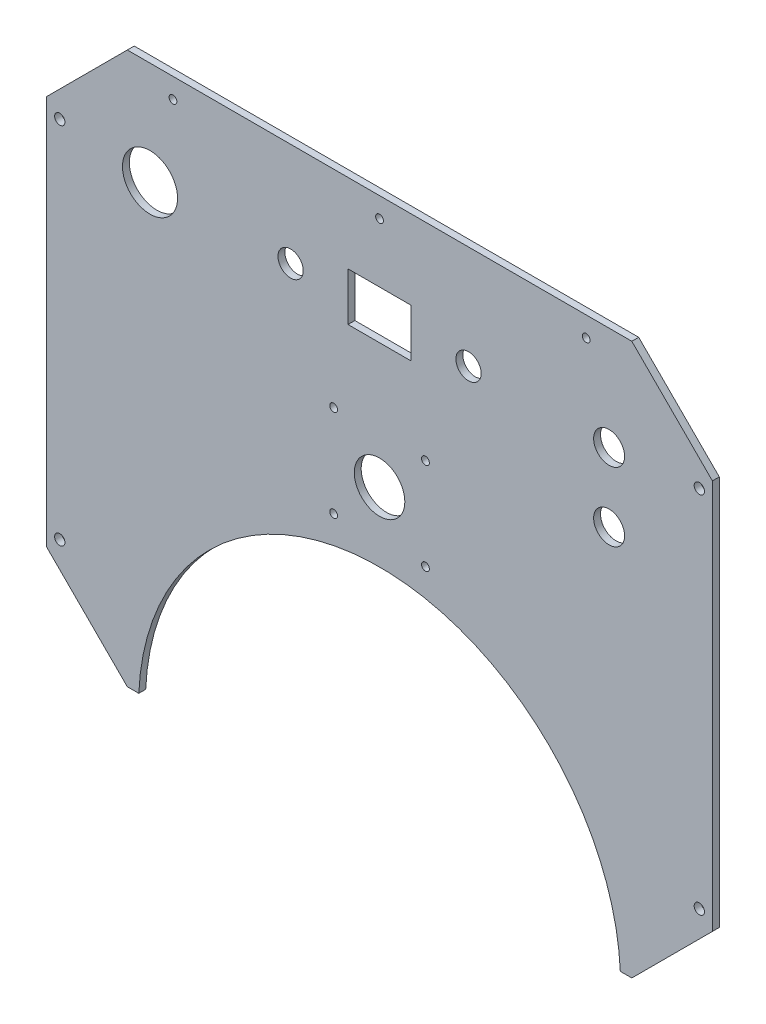
SolidWorks part; units mm, degrees
ref_plane "Plan de face" through (0, 0, 0) normal (0, 0, 1) x (1, 0, 0)
ref_plane "Plan de dessus" through (0, 0, 0) normal (0, 1, 0) x (1, 0, 0)
ref_plane "Plan de droite" through (0, 0, 0) normal (1, 0, 0) x (0, 0, -1)
sketch "Esquisse1" plane through (0, 0, 0) normal (0, 0, 1) x (1, 0, 0)
  line L0 (-145, 85) -> (-109.8862, 120.1138)
  line L1 (-109.8862, 120.1138) -> (-105, 125) construction
  line L2 (109.8862, 120.1138) -> (145, 85)
  line L3 (-85, 145) -> (85, 145) construction
  line L4 (105, -125) -> (109.8862, -120.1138) construction
  line L5 (-145, -145) -> (145, 145) construction
  line L6 (-145, 145) -> (145, -145) construction
  line L7 (85, 145) -> (105, 125) construction
  line L8 (-105, -125) -> (-85, -145) construction
  line L9 (-105, -125) -> (105, -125) construction
  line L10 (-105, 125) -> (105, 125) construction
  line L11 (85, -145) -> (105, -125) construction
  line L12 (-105, 125) -> (-85, 145) construction
  line L13 (105, 125) -> (109.8862, 120.1138) construction
  line L14 (-85, -145) -> (85, -145) construction
  line L15 (-109.8862, -120.1138) -> (-105, -125) construction
  line L16 (-109.8862, 120.1138) -> (109.8862, 120.1138)
  line L18 (-145, 0) -> (145, 0) construction
  line L19 (145, 85) -> (145, -85)
  line L20 (104.8862, -120.1138) -> (109.8862, -120.1138)
  line L21 (-109.8862, -120.1138) -> (-104.8862, -120.1138)
  line L22 (-145, 85) -> (-145, -85)
  line L24 (109.8862, -120.1138) -> (145, -85)
  line L25 (-145, -85) -> (-109.8862, -120.1138)
  line L28 (0, 125) -> (0, -125) construction
  arc A1 (-104.8862, -120.1138) -> (104.8862, -120.1138) centre (0, -125) cw
  point P0 (0, 0)
  point P30 (-145, 0)
  dimension "D1" = 290
  dimension "D2" = 290
  dimension "D6" = 60
  dimension "D7" = 60
extrude "Boss.-Extru.1" add sketch "Esquisse1" along normal blind 3
sketch "Esquisse21" plane through (0, 0, 3) normal (0, 0, 1) x (1, 0, 0)
  line L0 (0, 0) -> (191.7599, 0) construction
  line L1 (-145, 85) -> (-133.6, 85) construction
  line L2 (-145, 85) -> (-145, 73.6) construction
  line L3 (-145, 73.6) -> (-133.6, 73.6) construction
  line L4 (-133.6, 85) -> (-133.6, 73.6) construction
  line L5 (0, 0) -> (0, 158.3492) construction
  line L6 (145, 85) -> (145, 73.6) construction
  line L7 (145, 73.6) -> (133.6, 73.6) construction
  line L8 (133.6, 85) -> (133.6, 73.6) construction
  line L9 (145, 85) -> (133.6, 85) construction
  line L10 (-133.6, -85) -> (-133.6, -73.6) construction
  line L11 (-145, -73.6) -> (-133.6, -73.6) construction
  line L12 (-145, -85) -> (-145, -73.6) construction
  line L13 (-145, -85) -> (-133.6, -85) construction
  line L14 (145, -85) -> (145, -73.6) construction
  line L15 (145, -85) -> (133.6, -85) construction
  line L16 (145, -73.6) -> (133.6, -73.6) construction
  line L17 (133.6, -85) -> (133.6, -73.6) construction
  point P5 (-139.3, 79.3)
  point P9 (139.3, 79.3)
  point P19 (-139.3, -79.3)
  point P23 (139.3, -79.3)
  dimension "D1" = 11.4
  dimension "D2" = 11.4
  dimension "D3" = 5.7
  dimension "D4" = 5.7
hole_wizard "Dégagement M42" positions "Esquisse25" profile "Esquisse24" hole size "M4" standard "ISO"
sketch "Esquisse25" plane through (0, 0, 3) normal (0, 0, 1) x (1, 0, 0)
  point P1 (-139.3, 79.3)
  point P4 (-139.3, -79.3)
  point P7 (139.3, -79.3)
  point P10 (139.3, 79.3)
sketch "Esquisse24" plane through (-139.3, 79.3, 3) normal (1, 0, 0) x (0, -1, 0)
  line L0 (0, 0) -> (0, 11.3519)
  line L1 (0, 11.3519) -> (2.25, 10)
  line L2 (2.25, 10) -> (2.25, 0)
  line L5 (2.25, 0) -> (0, 0)
  line L10 (0, 11.3519) -> (-2.25, 10) construction
  line L11 (0, -6.35) -> (0, 107.95) construction
  dimension "Diamètre du perçage" = 4.5
  dimension "Profondeur du perçage" = 10
  dimension "Angle de pointe" = 118
sketch "Esquisse26" plane through (0, 0, 3) normal (0, 0, 1) x (1, 0, 0)
  line L0 (0, 0) -> (0, 158.3492) construction
  line L1 (-13.75, 85.6138) -> (13.75, 85.6138)
  line L2 (-13.75, 85.6138) -> (-13.75, 64.6138)
  line L3 (-13.75, 64.6138) -> (13.75, 64.6138)
  line L4 (-145, 85) -> (-145, -85) construction
  line L5 (109.8862, 120.1138) -> (-109.8862, 120.1138) construction
  line L6 (145, -85) -> (145, 85) construction
  line L7 (13.75, 85.6138) -> (13.75, 64.6138)
  line L8 (-13.75, 85.6138) -> (13.75, 64.6138) construction
  line L9 (-13.75, 64.6138) -> (13.75, 85.6138) construction
  circle A0 centre (-100, 75.1138) radius 20 construction
  point P2 (100, 75.1138)
  point P7 (70, 75.1138)
  point P10 (0, 75.1138)
  point P17 (-38.75, 75.1138)
  point P19 (38.75, 75.1138)
  dimension "D1" = 45
  dimension "D2" = 45
  dimension "D3" = 30
  dimension "D4" = 45
  dimension "D5" = 25
  dimension "D6" = 25
hole_wizard "Dégagement M221" positions "Esquisse28" profile "Esquisse27" hole size "M22" standard "ISO"
sketch "Esquisse28" plane through (0, 0, 3) normal (0, 0, 1) x (1, 0, 0)
  point P1 (-100, 75.1138)
sketch "Esquisse27" plane through (-100, 75.1138, 3) normal (1, 0, 0) x (0, -1, 0)
  line L0 (0, 0) -> (0, 17.2103)
  line L1 (0, 17.2103) -> (12, 10)
  line L2 (12, 10) -> (12, 0)
  line L5 (12, 0) -> (0, 0)
  line L10 (0, 17.2103) -> (-12, 10) construction
  line L11 (0, -6.35) -> (0, 107.95) construction
  dimension "Diamètre du perçage" = 24
  dimension "Profondeur du perçage" = 10
  dimension "Angle de pointe" = 118
hole_wizard "Dégagement M121" positions "Esquisse30" profile "Esquisse29" hole size "M12" standard "ISO"
sketch "Esquisse30" plane through (0, 0, 3) normal (0, 0, 1) x (1, 0, 0)
  point P4 (100, 75.1138)
  point P8 (100, 45.1138)
  dimension "D1" = 30
sketch "Esquisse29" plane through (100, 75.1138, 3) normal (1, 0, 0) x (0, -1, 0)
  line L0 (0, 0) -> (0, 14.0558)
  line L1 (0, 14.0558) -> (6.75, 10)
  line L2 (6.75, 10) -> (6.75, 0)
  line L5 (6.75, 0) -> (0, 0)
  line L10 (0, 14.0558) -> (-6.75, 10) construction
  line L11 (0, -6.35) -> (0, 107.95) construction
  dimension "Diamètre du perçage" = 13.5
  dimension "Profondeur du perçage" = 10
  dimension "Angle de pointe" = 118
hole_wizard "Dégagement M101" positions "Esquisse32" profile "Esquisse31" hole size "M10" standard "ISO"
sketch "Esquisse32" plane through (0, 0, 3) normal (0, 0, 1) x (1, 0, 0)
  point P1 (-38.75, 75.1138)
  point P7 (38.75, 75.1138)
sketch "Esquisse31" plane through (-38.75, 75.1138, 3) normal (1, 0, 0) x (0, -1, 0)
  line L0 (0, 0) -> (0, 13.3047)
  line L1 (0, 13.3047) -> (5.5, 10)
  line L2 (5.5, 10) -> (5.5, 0)
  line L5 (5.5, 0) -> (0, 0)
  line L10 (0, 13.3047) -> (-5.5, 10) construction
  line L11 (0, -6.35) -> (0, 107.95) construction
  dimension "Diamètre du perçage" = 11
  dimension "Profondeur du perçage" = 10
  dimension "Angle de pointe" = 118
extrude "Enlèv. mat.-Extru.1" cut sketch "Esquisse26" against normal blind 10 contours L1 L7 L3 L2
sketch "Esquisse33" plane through (0, 0, 3) normal (0, 0, 1) x (1, 0, 0)
  line L0 (-118.5862, 111.4138) -> (118.5862, 111.4138) construction
  line L1 (-109.8862, 120.1138) -> (-145, 85) construction
  line L2 (145, 85) -> (109.8862, 120.1138) construction
  line L3 (109.8862, 120.1138) -> (-109.8862, 120.1138) construction
  point P8 (0, 111.4138)
  point P9 (-90, 111.4138)
  point P10 (90, 111.4138)
  dimension "D1" = 8.7
  dimension "D2" = 90
  dimension "D3" = 90
hole_wizard "Dégagement M31" positions "Esquisse35" profile "Esquisse34" hole size "M3" standard "ISO" end condition through all
sketch "Esquisse35" plane through (0, 0, 3) normal (0, 0, 1) x (1, 0, 0)
  line L0 (-118.5862, 111.4138) -> (118.5862, 111.4138) construction
  point P1 (0, 111.4138)
  point P5 (-90, 111.4138)
  point P8 (90, 111.4138)
sketch "Esquisse34" plane through (0, 111.4138, 3) normal (1, 0, 0) x (0, -1, 0)
  line L0 (0, 0) -> (0, 3)
  line L1 (0, 3) -> (1.7, 3)
  line L2 (1.7, 3) -> (1.7, 0)
  line L5 (1.7, 0) -> (0, 0)
  line L11 (0, -6.35) -> (0, 107.95) construction
  dimension "Diamètre du perçage jusqu'au prochain" = 3.4
  dimension "Profondeur du perçage jusqu'au prochain" = 3
sketch "Esquisse42" plane through (0, 0, 3) normal (0, 0, 1) x (1, 0, 0)
  line L0 (109.8862, 120.1138) -> (-109.8862, 120.1138) construction
  line L1 (145, -85) -> (145, 85) construction
  line L3 (40, 50.1138) -> (-40, 50.1138) construction
  line L4 (40, 50.1138) -> (40, -29.8862) construction
  line L5 (40, -29.8862) -> (-40, -29.8862) construction
  line L6 (-40, 50.1138) -> (-40, -29.8862) construction
  line L7 (40, 50.1138) -> (-40, -29.8862) construction
  line L8 (40, -29.8862) -> (-40, 50.1138) construction
  point P0 (0, 10.1138)
  point P6 (0, 10.1138)
  dimension "D1" = 110
  dimension "D2" = 145
  dimension "D3" = 80
  dimension "D4" = 80
hole_wizard "Dégagement M201" positions "Esquisse44" profile "Esquisse43" hole size "M20" standard "ISO" end condition through all
sketch "Esquisse44" plane through (0, 0, 3) normal (0, 0, 1) x (1, 0, 0)
  point P1 (0, 10.1138)
sketch "Esquisse43" plane through (0, 10.1138, 3) normal (1, 0, 0) x (0, -1, 0)
  line L0 (0, 0) -> (0, 3)
  line L1 (0, 3) -> (11, 3)
  line L2 (11, 3) -> (11, 0)
  line L5 (11, 0) -> (0, 0)
  line L11 (0, -6.35) -> (0, 107.95) construction
  dimension "Diamètre du perçage jusqu'au prochain" = 22
  dimension "Profondeur du perçage jusqu'au prochain" = 3
sketch "Esquisse47" plane through (0, 0, 3) normal (0, 0, 1) x (1, 0, 0)
  line L1 (20, 30.1138) -> (-20, 30.1138) construction
  line L2 (20, 30.1138) -> (20, -9.8862) construction
  line L3 (20, -9.8862) -> (-20, -9.8862) construction
  line L4 (-20, 30.1138) -> (-20, -9.8862) construction
  line L5 (20, 30.1138) -> (-20, -9.8862) construction
  line L6 (20, -9.8862) -> (-20, 30.1138) construction
  point P0 (0, 10.1138)
  dimension "D1" = 40
  dimension "D2" = 40
hole_wizard "Dégagement M33" positions "Esquisse49" profile "Esquisse48" hole size "M3" standard "ISO" end condition through all
sketch "Esquisse49" plane through (0, 0, 3) normal (0, 0, 1) x (1, 0, 0)
  point P1 (-20, 30.1138)
  point P4 (20, 30.1138)
  point P7 (20, -9.8862)
  point P10 (-20, -9.8862)
sketch "Esquisse48" plane through (-20, 30.1138, 3) normal (1, 0, 0) x (0, -1, 0)
  line L0 (0, 0) -> (0, 3)
  line L1 (0, 3) -> (1.7, 3)
  line L2 (1.7, 3) -> (1.7, 0)
  line L5 (1.7, 0) -> (0, 0)
  line L11 (0, -6.35) -> (0, 107.95) construction
  dimension "Diamètre du perçage jusqu'au prochain" = 3.4
  dimension "Profondeur du perçage jusqu'au prochain" = 3
